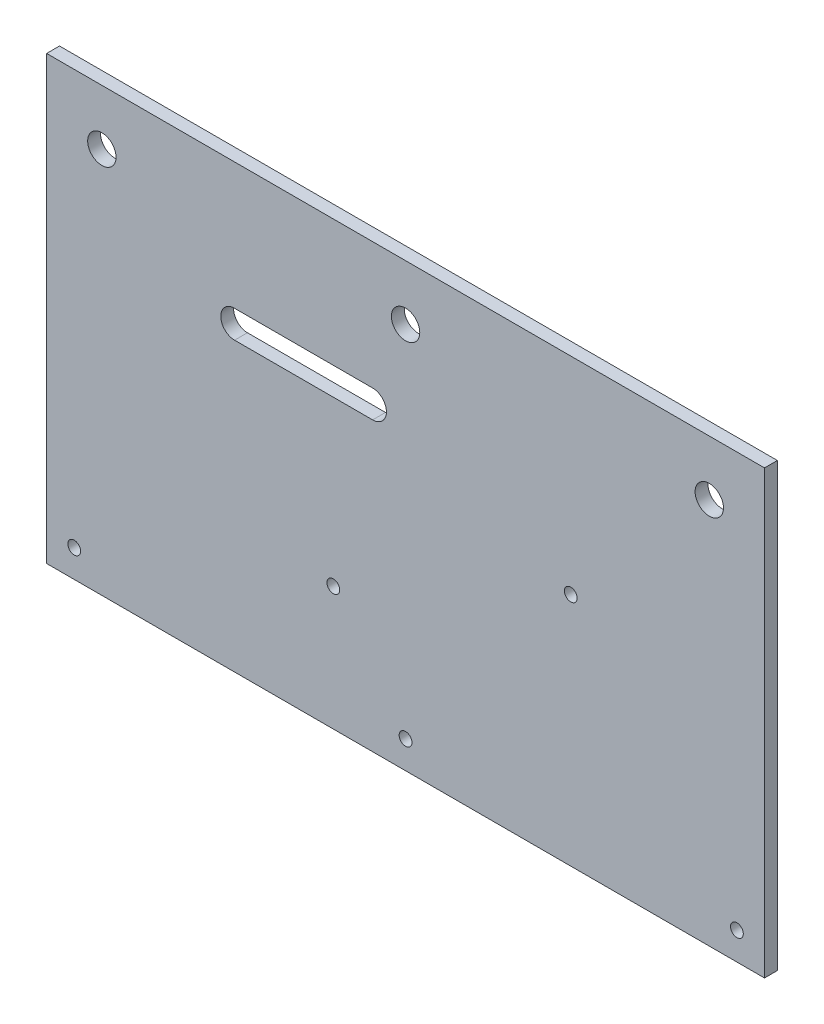
SolidWorks part; units mm, degrees
ref_plane "Front Plane" through (0, 0, 0) normal (0, 0, 1) x (1, 0, 0)
ref_plane "Top Plane" through (0, 0, 0) normal (0, 1, 0) x (1, 0, 0)
ref_plane "Right Plane" through (0, 0, 0) normal (1, 0, 0) x (0, 0, -1)
sketch "Sketch1" plane through (0, 0, 0) normal (0, 0, 1) x (1, 0, 0)
  line L0 (-82.55, 25.4) -> (82.55, 25.4) construction
  line L1 (-82.55, -50.8) -> (82.55, -50.8)
  line L2 (-82.55, -50.8) -> (-82.55, 50.8)
  line L3 (-82.55, 50.8) -> (82.55, 50.8)
  line L4 (82.55, -50.8) -> (82.55, 50.8)
  line L5 (-82.55, -50.8) -> (82.55, 50.8) construction
  line L6 (-82.55, 50.8) -> (82.55, -50.8) construction
  line L7 (-42.5, -40.7) -> (42.5, -40.7) construction
  line L8 (-42.5, -40.7) -> (-42.5, 15.3) construction
  line L9 (-42.5, 15.3) -> (42.5, 15.3) construction
  line L10 (42.5, -40.7) -> (42.5, 15.3) construction
  line L11 (0, 25.4) -> (0, -50.8) construction
  line L12 (0, -12.7) -> (42.5, -12.7) construction
  line L13 (-39.325, 18.475) -> (-7.575, 18.475) construction
  line L14 (-39.325, 21.65) -> (-7.575, 21.65)
  line L15 (-39.325, 15.3) -> (-7.575, 15.3)
  circle A0 centre (38, 3.3) radius 1.524 construction
  circle A1 centre (-16.61, -22.354) radius 1.524 construction
  arc A2 (-39.325, 21.65) -> (-39.325, 15.3) centre (-39.325, 18.475) ccw
  arc A3 (-7.575, 15.3) -> (-7.575, 21.65) centre (-7.575, 18.475) ccw
  point P0 (0, 0)
  point P20 (0, 15.3)
  point P23 (-23.45, 18.475)
  dimension "D3" = 3.048
  dimension "D12" = 3.175
  dimension "D1" = 165.1
  dimension "D2" = 101.6
  dimension "D4" = 54.61
  dimension "D5" = 25.654
  dimension "D6" = 85
  dimension "D7" = 56
  dimension "D8" = 4.5
  dimension "D9" = 12
  dimension "D10" = 25.4
  dimension "D11" = 31.75
extrude "Boss-Extrude1" add sketch "Sketch1" along normal mid plane 2.9591 contours L1 L4 L3 L2 A3 L15 A2 L14
hole_wizard "1/4 Clearance Hole1" positions "Sketch5" profile "Sketch4" hole size "1/4" standard "ANSI Inch" end condition through all
sketch "Sketch5" plane through (-54.2806, -28.3096, 1.4796) normal (0, 0, 1) x (1, 0, 0)
  line L3 (-28.2694, -22.4904) -> (-28.2694, 79.1096) construction
  line L4 (136.8306, -22.4904) -> (136.8306, 79.1096) construction
  line L5 (-28.2694, 79.1096) -> (136.8306, 79.1096) construction
  point P0 (-15.5694, 66.4096)
  point P2 (124.1306, 66.4096)
  point P11 (54.2806, 66.4096)
  dimension "D1" = 12.7
  dimension "D2" = 12.7
  dimension "D3" = 12.7
sketch "Sketch4" plane through (-69.85, 38.1, 1.4796) normal (1, 0, 0) x (0, -1, 0)
  line L0 (0, 0) -> (0, 2.9591)
  line L1 (0, 2.9591) -> (3.2639, 2.9591)
  line L2 (3.2639, 2.9591) -> (3.2639, 0)
  line L5 (3.2639, 0) -> (0, 0)
  line L11 (0, -6.35) -> (0, 107.95) construction
  dimension "Thru Hole Dia." = 6.5278
  dimension "Thru Hole Depth" = 2.9591
hole_wizard "#4 Clearance Hole1" positions "Sketch7" profile "Sketch6" hole size "#4" standard "ANSI Inch" end condition through all
sketch "Sketch7" plane through (-67.9317, 13.6303, 1.4796) normal (0, 0, 1) x (1, 0, 0)
  line L3 (150.4817, -64.4303) -> (150.4817, 37.1697) construction
  line L4 (-14.6183, -64.4303) -> (150.4817, -64.4303) construction
  line L5 (-14.6183, -64.4303) -> (-14.6183, 37.1697) construction
  line L6 (-8.2683, -58.0803) -> (144.1317, -58.0803) construction
  point P0 (105.9317, -10.3303)
  point P3 (51.3217, -35.9843)
  point P7 (-8.2683, -58.0803)
  point P9 (144.1317, -58.0803)
  point P29 (67.9317, -58.0803)
  dimension "D1" = 6.35
  dimension "D2" = 6.35
  dimension "D3" = 6.35
  dimension "D4" = 6.35
sketch "Sketch6" plane through (38, 3.3, 1.4796) normal (1, 0, 0) x (0, -1, 0)
  line L0 (0, 0) -> (0, 2.9591)
  line L1 (0, 2.9591) -> (1.4732, 2.9591)
  line L2 (1.4732, 2.9591) -> (1.4732, 0)
  line L5 (1.4732, 0) -> (0, 0)
  line L11 (0, -6.35) -> (0, 107.95) construction
  dimension "Thru Hole Dia." = 2.9464
  dimension "Thru Hole Depth" = 2.9591
